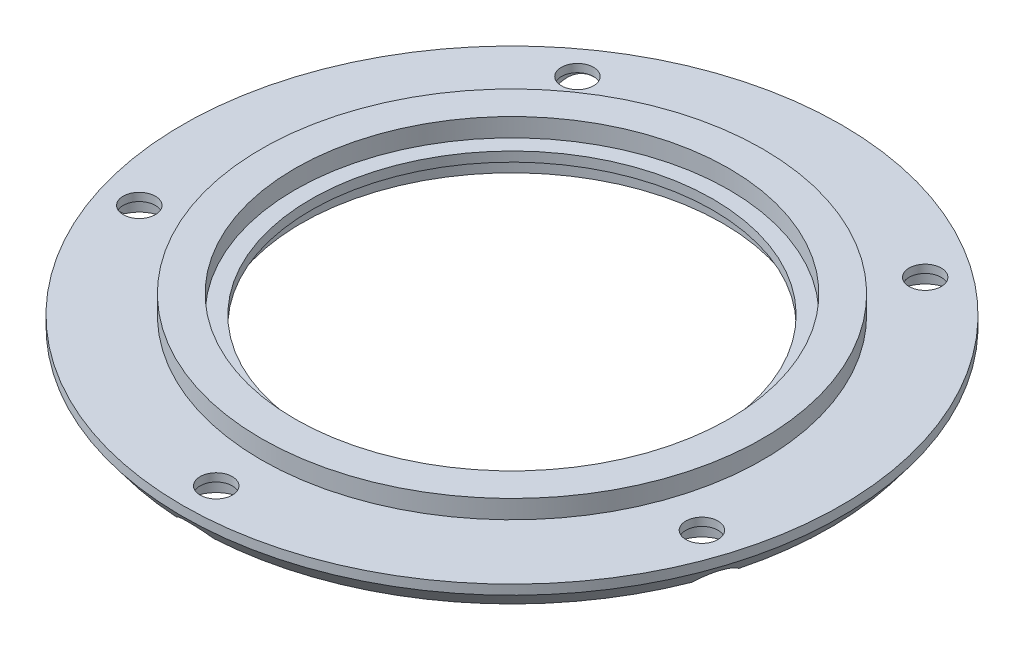
SolidWorks part; units mm, degrees
ref_plane "Plan de face" through (0, 0, 0) normal (0, 0, 1) x (1, 0, 0)
ref_plane "Plan de dessus" through (0, 0, 0) normal (0, 1, 0) x (1, 0, 0)
ref_plane "Plan de droite" through (0, 0, 0) normal (1, 0, 0) x (0, 0, -1)
sketch "Esquisse1" plane through (0, 0, 0) normal (1, 0, 0) x (0, 0, -1)
  line L0 (0, -40.8786) -> (0, 70.0105) construction
  line L1 (-13.5, 0) -> (-13.5, 1.15)
  line L2 (-13.5, 1.15) -> (-15.6, 1.15)
  line L3 (-15.6, 1.15) -> (-15.6, 0)
  line L4 (-15.6, 0) -> (-20.5, 0)
  line L5 (-20.5, 0) -> (-20.5, -0.6)
  line L6 (-19.75, -1.6) -> (-13.1, -1.6)
  line L7 (-13.1, -1.6) -> (-13.1, -0.6)
  line L8 (-13.1, -0.6) -> (-12.5, -0.6)
  line L9 (-12.5, -0.6) -> (-12.5, 0)
  line L10 (-12.5, 0) -> (-13.5, 0)
  line L11 (-20.5, -0.6) -> (-19.75, -1.6)
  dimension "D1" = 12.5
  dimension "D2" = 0.6
  dimension "D3" = 0.6
  dimension "D4" = 1
  dimension "D5" = 13.5
  dimension "D6" = 1.15
  dimension "D7" = 15.6
  dimension "D8" = 20.5
  dimension "D9" = 0.75
revolve "Révolution1" add sketch "Esquisse1" angle 360 about L0
sketch "Esquisse2" plane through (0, 0, 0) normal (0, 1, 0) x (1, 0, 0)
  line L0 (0, 0) -> (0, -11.1301) construction
  line L1 (0, 0) -> (9.578, -3.1121) construction
  line L2 (0, 0) -> (6.221, 8.5625) construction
  line L3 (0, 0) -> (-5.4986, 7.5682) construction
  line L4 (0, 0) -> (-10.2381, -3.3266) construction
  circle A0 centre (0, -18.4) radius 1
  circle A1 centre (17.4994, -5.6859) radius 1
  circle A2 centre (10.8152, 14.8859) radius 1
  circle A3 centre (-10.8152, 14.8859) radius 1
  circle A4 centre (-17.4994, -5.6859) radius 1
  dimension "D5" = 18.4
  dimension "D6" = 18.4
  dimension "D1" = 72
  dimension "D2" = 72
  dimension "D3" = 72
  dimension "D4" = 72
  dimension "D7" = 18.4
  dimension "D8" = 18.4
  dimension "D9" = 18.4
extrude "Enlèv. mat.-Extru.1" cut sketch "Esquisse2" against normal through all
sketch "Esquisse3" plane through (0, -1.6, 0) normal (0, -1, 0) x (1, 0, 0)
  circle A0 centre (0, 18.4) radius 1.75
  circle A1 centre (17.4994, 5.6859) radius 1.75
  circle A2 centre (10.8152, -14.8859) radius 1.75
  circle A3 centre (-10.8152, -14.8859) radius 1.75
  circle A4 centre (-17.4994, 5.6859) radius 1.75
  point P15 (0, 0)
  dimension "D1" = 5
extrude "Enlèv. mat.-Extru.2" cut sketch "Esquisse3" against normal blind 1.1
